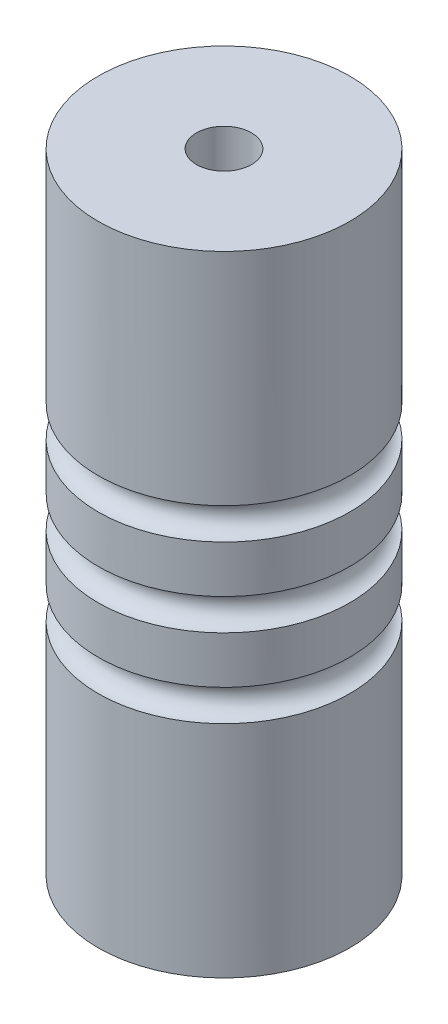
SolidWorks part; units mm, degrees
ref_plane "Front Plane" through (0, 0, 0) normal (0, 0, 1) x (1, 0, 0)
ref_plane "Top Plane" through (0, 0, 0) normal (0, 1, 0) x (1, 0, 0)
ref_plane "Right Plane" through (0, 0, 0) normal (1, 0, 0) x (0, 0, -1)
sketch "Sketch1" plane through (0, 0, 0) normal (0, 1, 0) x (1, 0, 0)
  circle A0 centre (0, 0) radius 8
extrude "Extrude1" add sketch "Sketch1" along normal blind 40
sketch "Sketch2" plane through (0, 40, 0) normal (0, 1, 0) x (-1, 0, 0)
  circle A0 centre (0, 0) radius 1.75
extrude "Extrude2" cut sketch "Sketch2" against normal blind 40
sketch "Sketch3" plane through (0, 0, 0) normal (0, -1, 0) x (1, 0, 0)
  circle A0 centre (0, 0) radius 4
extrude "Extrude3" cut sketch "Sketch3" against normal blind 6.35
sketch "Sketch4" plane through (0, 0, 0) normal (0, 0, 1) x (1, 0, 0)
  line L0 (8, 0) -> (8, 40) construction
  circle A0 centre (8, 20) radius 1
  circle A1 centre (8, 25) radius 1
  circle A2 centre (8, 15) radius 1
ref_plane "Plane1" through (0, 15, 0) normal (0, 1, 0) x (-1, 0, 0)
sketch "Sketch6" plane through (0, 15, 0) normal (0, 1, 0) x (-1, 0, 0)
  circle A0 centre (0, 0) radius 8
sweep "Cut-Sweep1" cut profiles "Sketch4" path "Sketch6"
